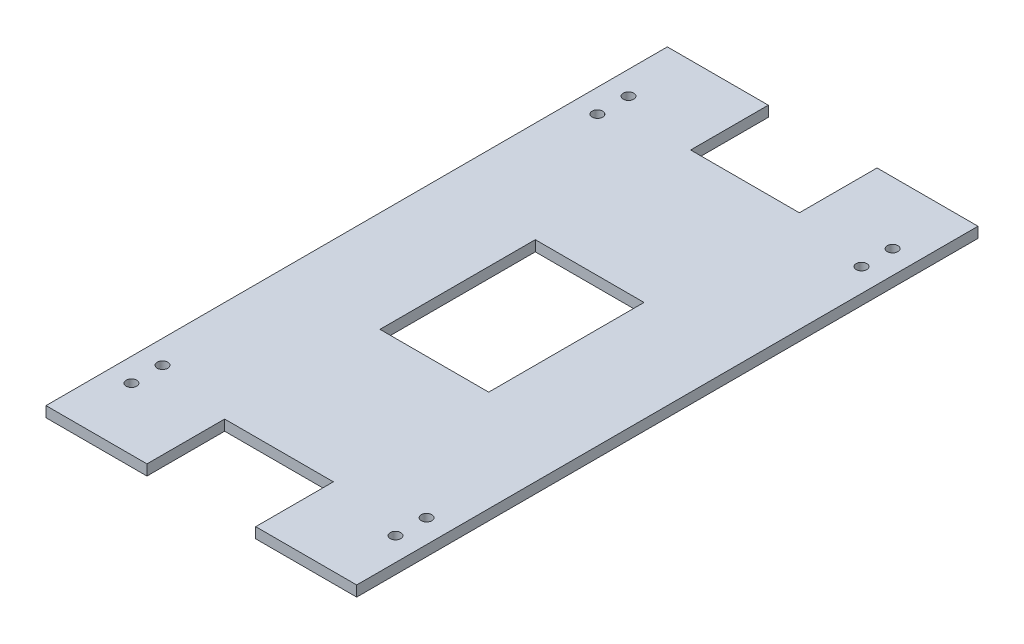
SolidWorks part; units mm, degrees
ref_plane "Alzado" through (0, 0, 0) normal (0, 0, 1) x (1, 0, 0)
ref_plane "Planta" through (0, 0, 0) normal (0, 1, 0) x (1, 0, 0)
ref_plane "Vista lateral" through (0, 0, 0) normal (1, 0, 0) x (0, 0, -1)
sketch "Croquis1" plane through (0, 0, 0) normal (0, 1, 0) x (1, 0, 0)
  line L1 (-50, 100) -> (50, 100)
  line L2 (-50, 100) -> (-50, -100)
  line L3 (-50, -100) -> (50, -100)
  line L4 (50, 100) -> (50, -100)
  line L5 (-50, 100) -> (50, -100) construction
  line L6 (-50, -100) -> (50, 100) construction
  point P0 (0, 0)
  dimension "D1" = 100
  dimension "D2" = 200
extrude "Saliente-Extruir1" add sketch "Croquis1" along normal blind 3.4
sketch "Croquis2" plane through (0, 3.4, 0) normal (0, 1, 0) x (1, 0, 0)
  line L0 (30, -100) -> (30, -85.4321) construction
  line L1 (-50, -100) -> (50, -100) construction
  line L2 (0, 0) -> (0, -114.8957) construction
  line L3 (0, 0) -> (37.2153, 0) construction
  line L4 (-50, 100) -> (-50, -100) construction
  line L9 (50, 100) -> (-50, 100) construction
  line L10 (-17.5, 100) -> (17.5, 100)
  line L11 (-17.5, 100) -> (-17.5, 75)
  line L12 (-17.5, 75) -> (17.5, 75)
  line L13 (17.5, 100) -> (17.5, 75)
  line L14 (50, 100) -> (-50, 100) construction
  line L15 (-17.5, 25) -> (17.5, 25)
  line L16 (-17.5, 25) -> (-17.5, -25)
  line L17 (-17.5, -25) -> (17.5, -25)
  line L18 (17.5, 25) -> (17.5, -25)
  line L19 (-50, 100) -> (-50, -100) construction
  line L20 (17.5, -100) -> (17.5, -75)
  line L21 (-17.5, -75) -> (17.5, -75)
  line L22 (-17.5, -100) -> (-17.5, -75)
  line L23 (-17.5, -100) -> (17.5, -100)
  circle A0 centre (42.5, -80) radius 1.7
  circle A1 centre (42.5, -70) radius 1.7
  circle A2 centre (-42.5, -80) radius 1.7
  circle A3 centre (-42.5, -70) radius 1.7
  circle A4 centre (42.5, 70) radius 1.7
  circle A5 centre (42.5, 80) radius 1.7
  circle A6 centre (-42.5, 70) radius 1.7
  circle A7 centre (-42.5, 80) radius 1.7
  point P22 (0, 100)
  point P23 (0, 100)
  point P36 (0, -25)
  point P39 (-17.5, 0)
  point P40 (-50, 0)
  dimension "D2" = 3.4
  dimension "D1" = 10
  dimension "D3" = 30
  dimension "D4" = 12.5
  dimension "D5" = 20
  dimension "D6" = 25
  dimension "D7" = 35
  dimension "D8" = 35
  dimension "D9" = 50
extrude "Cortar-Extruir1" cut sketch "Croquis2" against normal up to surface (3.4 mm away) up to face at (0, 0, 0)
